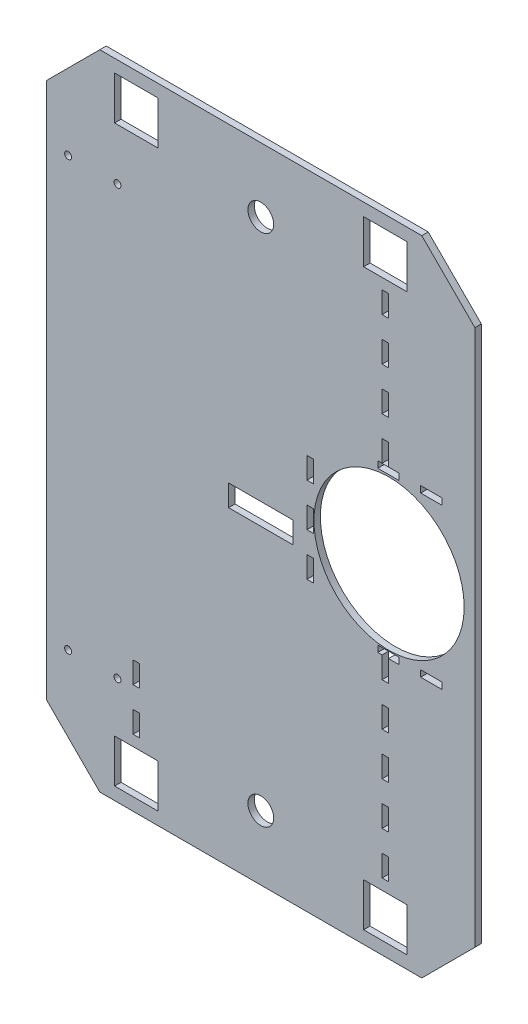
SolidWorks part; units mm, degrees
material "Alliage 1060"
ref_plane "Plan de dessus" through (0, 0, 0) normal (0, 0, 1) x (1, 0, 0)
ref_plane "Plan de droite" through (0, 0, 0) normal (0, 1, 0) x (1, 0, 0)
ref_plane "Plan de face" through (0, 0, 0) normal (1, 0, 0) x (0, 0, -1)
sketch "Esquisse1" plane through (0, 0, 0) normal (0, 0, 1) x (1, 0, 0)
  line L0 (0, 0) -> (-150, 0)
  line L1 (-150, 0) -> (-174.7487, 24.7487)
  line L2 (-174.7487, 24.7487) -> (-174.7487, 274.7487)
  line L3 (-174.7487, 274.7487) -> (-150, 299.4975)
  line L4 (-150, 299.4975) -> (0, 299.4975)
  line L5 (0, 299.4975) -> (24.7487, 274.7487)
  line L6 (24.7487, 274.7487) -> (24.7487, 24.7487)
  line L7 (24.7487, 24.7487) -> (0, 0)
  line L9 (-150, 299.4975) -> (0, 299.4975)
  line L10 (-174.7487, 274.7487) -> (-174.7487, 24.7487)
  line L12 (24.7487, 274.7487) -> (24.7487, 24.7487)
  dimension "D1" = 250
  dimension "D2" = 35
  dimension "D3" = 135
  dimension "D4" = 150
extrude "Base" add sketch "Esquisse1" along normal blind 3 contours L7 L6 L5 L4 L3 L2 L1 L0
sketch "Esquisse3" plane through (0, 0, 3) normal (0, 0, 1) x (1, 0, 0)
  line L0 (-174.7487, 24.7487) -> (-174.7487, 274.7487) construction
  line L1 (-143.0987, 5.9) -> (-122.8987, 5.9)
  line L2 (-143.0987, 5.9) -> (-143.0987, 26.1)
  line L3 (-143.0987, 26.1) -> (-122.8987, 26.1)
  line L4 (-122.8987, 5.9) -> (-122.8987, 26.1)
  line L5 (0, 0) -> (-150, 0) construction
  dimension "D1" = 20.2
  dimension "D2" = 31.65
  dimension "D3" = 5.9
extrude "Enlèv. mat.-Extru.1" cut sketch "Esquisse3" against normal through all
pattern_linear "Répétition linéaire1" count 2 spacing 267.5 along (0, 1, 0) count 2 spacing 116 along (1, 0, 0) of "Enlèv. mat.-Extru.1"
sketch "Esquisse4" plane through (0, 0, 3) normal (0, 0, 1) x (1, 0, 0)
  line L0 (24.7487, 274.7487) -> (24.7487, 24.7487) construction
  line L1 (-150, 299.4975) -> (0, 299.4975) construction
  circle A0 centre (-15.2513, 159.4975) radius 35
  dimension "D1" = 70
  dimension "D2" = 40
  dimension "D3" = 140
extrude "Enlèv. mat.-Extru.2" cut sketch "Esquisse4" against normal through all
sketch "Esquisse5" plane through (0, 0, 3) normal (0, 0, 1) x (1, 0, 0)
  line L0 (0, 0) -> (-150, 0) construction
  line L1 (-150, 299.4975) -> (0, 299.4975) construction
  line L2 (-174.7487, 24.7487) -> (-174.7487, 274.7487) construction
  line L3 (-90, 144.7487) -> (-60, 144.7487)
  line L4 (-90, 144.7487) -> (-90, 154.7487)
  line L5 (-90, 154.7487) -> (-60, 154.7487)
  line L6 (-60, 144.7487) -> (-60, 154.7487)
  circle A0 centre (-75, 30) radius 6
  circle A1 centre (-75, 269.4975) radius 6
  point P5 (-75, 0)
  point P15 (-174.7487, 149.7487)
  point P16 (-90, 149.7487)
  point P17 (-75, 144.7487)
  dimension "D1" = 12
  dimension "D3" = 12
  dimension "D2" = 30
  dimension "D4" = 30
  dimension "D5" = 10
  dimension "D6" = 30
extrude "Enlèv. mat.-Extru.3" cut sketch "Esquisse5" against normal through all
sketch "Esquisse6" plane through (0, 0, 3) normal (0, 0, 1) x (1, 0, 0)
  line L0 (-174.7487, 24.7487) -> (-174.7487, 274.7487) construction
  line L1 (-150, 299.4975) -> (0, 299.4975) construction
  line L2 (24.7487, 149.7487) -> (-174.7487, 149.7487) construction
  line L3 (24.7487, 274.7487) -> (24.7487, 24.7487) construction
  circle A0 centre (-164.7487, 249.4975) radius 1.625
  circle A1 centre (-141.7487, 249.4975) radius 1.625
  circle A2 centre (-164.7487, 50) radius 1.625
  circle A3 centre (-141.7487, 50) radius 1.625
  dimension "D1" = 3.25
  dimension "D2" = 3.25
  dimension "D3" = 23
  dimension "D4" = 10
  dimension "D5" = 50
extrude "Enlèv. mat.-Extru.4" cut sketch "Esquisse6" against normal through all
sketch "Sketch1" plane through (0, 0, 3) normal (0, 0, 1) x (1, 0, 0)
  line L0 (-27.0987, 273.4) -> (-6.8987, 273.4) construction
  line L1 (-18.4987, 268.4) -> (-15.4987, 268.4)
  line L2 (-18.4987, 268.4) -> (-18.4987, 258.4)
  line L3 (-18.4987, 258.4) -> (-15.4987, 258.4)
  line L4 (-15.4987, 268.4) -> (-15.4987, 258.4)
  line L5 (-16.9987, 273.4) -> (-16.9987, 293.6) construction
  line L6 (-6.8987, 293.6) -> (-27.0987, 293.6) construction
  line L7 (-16.9987, 268.4) -> (-16.9987, 258.4) construction
  dimension "D1" = 3
  dimension "D2" = 10
  dimension "D3" = 5
  dimension "D4" = 0
extrude "Cut-Extrude1" cut sketch "Sketch1" against normal through all
pattern_linear "LPattern1" count 4 spacing 20 along (0, -1, 0) of "Cut-Extrude1"
sketch "Sketch2" plane through (0, 0, 3) normal (0, 0, 1) x (1, 0, 0)
  line L0 (-15.4987, 198.4) -> (-15.4987, 208.4) construction
  line L1 (-18.4987, 31.1) -> (-15.4987, 31.1)
  line L2 (-18.4987, 31.1) -> (-18.4987, 41.1)
  line L3 (-18.4987, 41.1) -> (-15.4987, 41.1)
  line L4 (-15.4987, 31.1) -> (-15.4987, 41.1)
  line L5 (-6.8987, 26.1) -> (-27.0987, 26.1) construction
  dimension "D1" = 3
  dimension "D2" = 10
  dimension "D3" = 5
extrude "Cut-Extrude2" cut sketch "Sketch2" against normal through all
pattern_linear "LPattern2" count 5 spacing 20 along (0, 1, 0) of "Cut-Extrude2"
sketch "Sketch4" plane through (0, 0, 3) normal (0, 0, 1) x (1, 0, 0)
  line L0 (-132.9987, 31.1) -> (-132.9987, 41.1) construction
  line L1 (-134.4987, 31.1) -> (-131.4987, 31.1)
  line L2 (-134.4987, 31.1) -> (-134.4987, 41.1)
  line L3 (-134.4987, 41.1) -> (-131.4987, 41.1)
  line L4 (-131.4987, 31.1) -> (-131.4987, 41.1)
  line L5 (-132.9987, 5.9) -> (-132.9987, 26.1) construction
  line L6 (-143.0987, 5.9) -> (-122.8987, 5.9) construction
  line L7 (-122.8987, 26.1) -> (-143.0987, 26.1) construction
  dimension "D1" = 0
  dimension "D2" = 5
  dimension "D3" = 10
  dimension "D4" = 3
extrude "Cut-Extrude3" cut sketch "Sketch4" against normal through all
pattern_linear "LPattern3" count 2 spacing 20 along (0, 1, 0) of "Cut-Extrude3"
sketch "Esquisse7" plane through (0, 0, 3) normal (0, 0, 1) x (1, 0, 0)
  line L0 (9.4987, 122.6) -> (24.7487, 122.6) construction
  line L1 (-0.5013, 124.1) -> (9.4987, 124.1)
  line L2 (-0.5013, 124.1) -> (-0.5013, 121.1)
  line L3 (-0.5013, 121.1) -> (9.4987, 121.1)
  line L4 (9.4987, 124.1) -> (9.4987, 121.1)
  line L5 (-20.5013, 195.3975) -> (-10.5013, 195.3975)
  line L6 (-0.5013, 195.3975) -> (9.4987, 195.3975)
  line L7 (-0.5013, 124.1) -> (9.4987, 121.1) construction
  line L8 (9.4987, 124.1) -> (-0.5013, 121.1) construction
  line L9 (24.7487, 274.7487) -> (24.7487, 24.7487) construction
  line L10 (0, 0) -> (-150, 0) construction
  line L11 (-20.5013, 124.1) -> (-10.5013, 124.1)
  line L12 (-20.5013, 124.1) -> (-20.5013, 121.1)
  line L13 (-20.5013, 121.1) -> (-10.5013, 121.1)
  line L14 (-10.5013, 124.1) -> (-10.5013, 121.1)
  line L15 (-20.5013, 124.1) -> (-10.5013, 121.1) construction
  line L16 (-10.5013, 124.1) -> (-20.5013, 121.1) construction
  line L23 (9.4987, 196.8975) -> (24.7487, 196.8975) construction
  line L24 (-0.5013, 195.3975) -> (-0.5013, 198.3975)
  line L25 (-0.5013, 198.3975) -> (9.4987, 198.3975)
  line L26 (9.4987, 195.3975) -> (9.4987, 198.3975)
  line L27 (-20.5013, 195.3975) -> (-20.5013, 198.3975)
  line L28 (-20.5013, 198.3975) -> (-10.5013, 198.3975)
  line L29 (-10.5013, 195.3975) -> (-10.5013, 198.3975)
  line L43 (-150, 299.4975) -> (0, 299.4975) construction
  line L47 (-40.5013, 124.1) -> (-30.5013, 124.1) [skipped]
  line L48 (-40.5013, 124.1) -> (-40.5013, 121.1) [skipped]
  line L49 (-40.5013, 121.1) -> (-30.5013, 121.1) [skipped]
  line L50 (-30.5013, 124.1) -> (-30.5013, 121.1) [skipped]
  line L51 (-40.5013, 124.1) -> (-30.5013, 121.1) construction
  line L52 (-30.5013, 124.1) -> (-40.5013, 121.1) construction
  line L53 (-40.5013, 195.3975) -> (-30.5013, 195.3975) [skipped]
  line L54 (-40.5013, 195.3975) -> (-40.5013, 198.3975) [skipped]
  line L55 (-40.5013, 198.3975) -> (-30.5013, 198.3975) [skipped]
  line L56 (-30.5013, 195.3975) -> (-30.5013, 198.3975) [skipped]
  point P26 (9.4987, 196.8975)
  dimension "D1" = 3
  dimension "D2" = 10
  dimension "D3" = 15.25
  dimension "D4" = 122.6
  dimension "D6" = 10
  dimension "D7" = 102.6
  dimension "D8" = 10
  dimension "D9" = 3
  dimension "D10" = 15.25
  dimension "D12" = 10
  dimension "D5" = 3
  dimension "D11" = 3
extrude "Enlèv. mat.-Extru.5" cut sketch "Esquisse7" against normal blind 3
sketch "Esquisse8" plane through (0, 0, 3) normal (0, 0, 1) x (1, 0, 0)
  line L0 (-20.5013, 124.1) -> (-20.5013, 134.1) construction
  line L9 (-50.5013, 134.1) -> (-20.5013, 134.1) construction
  line L10 (-50.5013, 154.1) -> (-53.5013, 154.1)
  line L13 (-50.5013, 134.1) -> (-53.5013, 134.1)
  line L14 (-50.5013, 134.1) -> (-50.5013, 144.1)
  line L15 (-50.5013, 144.1) -> (-53.5013, 144.1)
  line L16 (-53.5013, 134.1) -> (-53.5013, 144.1)
  line L17 (-50.5013, 154.1) -> (-50.5013, 164.1)
  line L18 (-50.5013, 164.1) -> (-53.5013, 164.1)
  line L19 (-53.5013, 154.1) -> (-53.5013, 164.1)
  line L20 (-50.5013, 174.1) -> (-53.5013, 174.1)
  line L21 (-50.5013, 174.1) -> (-50.5013, 184.1)
  line L22 (-50.5013, 184.1) -> (-53.5013, 184.1)
  line L23 (-53.5013, 174.1) -> (-53.5013, 184.1)
  dimension "D1" = 30
  dimension "D2" = 10
  dimension "D3" = 10
  dimension "D4" = 3
  dimension "D6" = 10
  dimension "D5" = 3
extrude "Enlèv. mat.-Extru.6" cut sketch "Esquisse8" against normal blind 3
